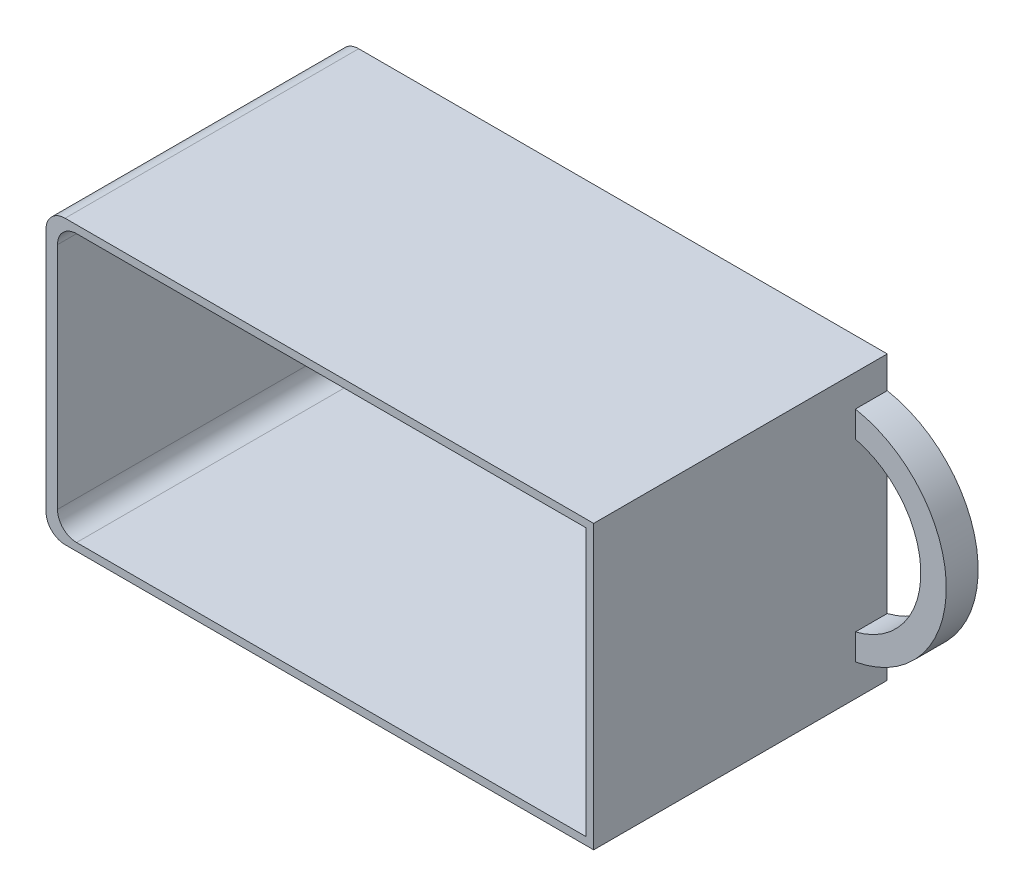
SolidWorks part; units mm, degrees
ref_plane "Спереди" through (0, 0, 0) normal (0, 0, 1) x (1, 0, 0)
ref_plane "Сверху" through (0, 0, 0) normal (0, 1, 0) x (1, 0, 0)
ref_plane "Справа" through (0, 0, 0) normal (1, 0, 0) x (0, 0, -1)
other "Configuration Table"
sketch "Эскиз1" plane through (0, 0, 0) normal (0, 0, 1) x (1, 0, 0)
  line L1 (-43, -22.2) -> (43, -22.2)
  line L2 (-43, -22.2) -> (-43, 22.2)
  line L3 (-43, 22.2) -> (43, 22.2)
  line L4 (43, -22.2) -> (43, 22.2)
  line L5 (-43, -22.2) -> (43, 22.2) construction
  line L6 (-43, 22.2) -> (43, -22.2) construction
  point P0 (0, 0)
  dimension "D1" = 86
  dimension "D2" = 44.4
extrude "Бобышка-Вытянуть1" add sketch "Эскиз1" along normal blind 46.1
sketch "Эскиз2" plane through (0, 0, 0) normal (0, 0, 1) x (1, 0, 0)
  line L0 (0, 0) -> (43, 0) construction
  line L1 (43, -22.2) -> (43, 22.2) construction
  line L2 (43, 13.1088) -> (43, 17.2)
  line L3 (43, -17.2) -> (43, -13.1088)
  arc A0 (43, -17.2) -> (43, 17.2) centre (39.7735, 0) ccw
  arc A1 (43, -13.1088) -> (43, 13.1088) centre (39.7735, 0) ccw
  point P8 (53.2735, 0)
  dimension "D3" = 13.5
  dimension "D4" = 4
  dimension "D1" = 5
  dimension "D2" = 5
  dimension "D5" = 10.2735
extrude "Бобышка-Вытянуть2" add sketch "Эскиз2" along normal blind 5
sketch "Эскиз3" plane through (0, 0, 46.1) normal (0, 0, 1) x (1, 0, 0)
  line L5 (-41.2, 22.2) -> (-41.2, -22.2)
  line L6 (-43, -21) -> (41.8, -21)
  line L7 (41.8, -21) -> (41.8, 21)
  line L8 (41.8, 21) -> (-43, 21)
  line L9 (-41.2, -21) -> (41.8, -21)
  line L10 (41.8, -21) -> (41.8, 21)
  line L11 (41.8, 21) -> (-41.2, 21)
  line L12 (-41.2, 21) -> (-41.2, -21)
  dimension "D1" = 1.2
  dimension "D2" = 1.8
extrude "Вырез-Вытянуть1" cut sketch "Эскиз3" against normal offset from surface (44.9 mm away) 1.2 up to face at (48.1368, 0, 0)
fillet "Скругление1" radius 3 4 edges at (-43, -22.2, 23.05) (-43, 22.2, 23.05) (-41.2, 21, 23.65) (-41.2, -21, 23.65)
